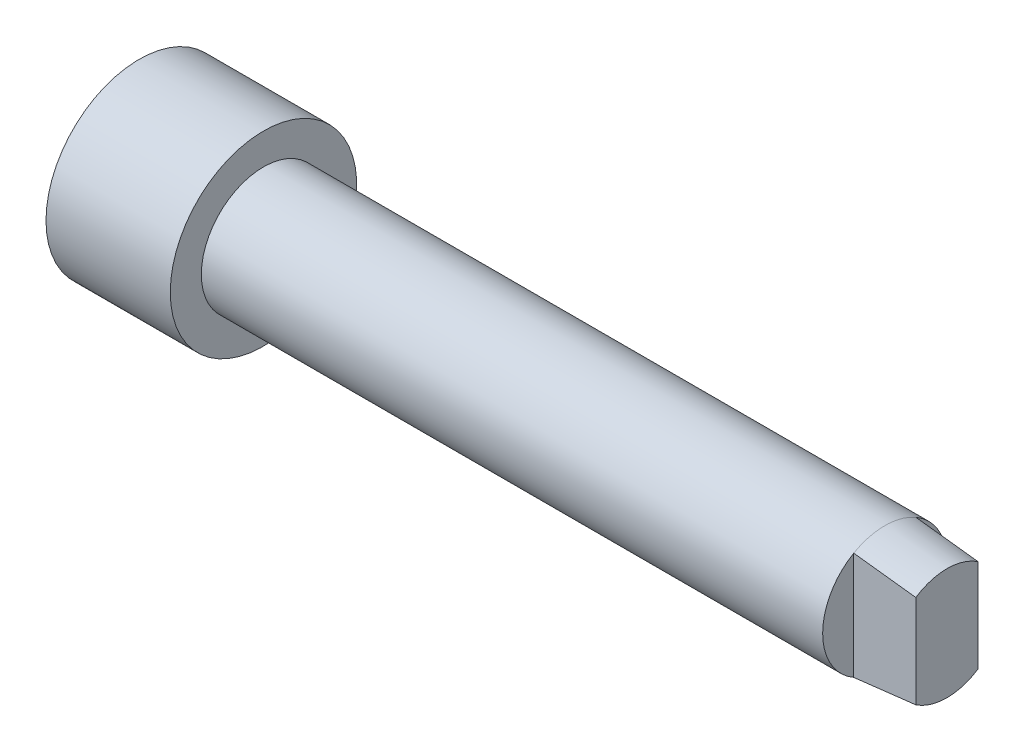
SolidWorks part; units mm, degrees
ref_plane "Front Plane" through (0, 0, 0) normal (0, 0, 1) x (1, 0, 0)
ref_plane "Top Plane" through (0, 0, 0) normal (0, 1, 0) x (1, 0, 0)
ref_plane "Right Plane" through (0, 0, 0) normal (1, 0, 0) x (0, 0, -1)
sketch "Sketch1" plane through (0, 0, 0) normal (0, 0, 1) x (1, 0, 0)
  line L0 (0, 0) -> (55, 0)
  line L1 (55, 0) -> (55, 4.5)
  line L2 (55, 4.5) -> (50, 5)
  line L3 (50, 5) -> (0, 5)
  line L4 (0, 5) -> (0, 0)
  line L5 (0, 5) -> (0, 7.5)
  line L6 (0, 7.5) -> (-10, 7.5)
  line L7 (-10, 7.5) -> (-10, 5)
  line L8 (-10, 5) -> (-5, 5)
  line L9 (-5, 5) -> (-5, 0)
  line L10 (-5, 0) -> (0, 0)
  dimension "D1" = 55
  dimension "D2" = 4.5
  dimension "D3" = 5
  dimension "D4" = 5
  dimension "D5" = 2.5
  dimension "D6" = 10
  dimension "D7" = 5
revolve "Revolve1" add sketch "Sketch1" angle 360 about L0
sketch "Sketch2" plane through (55, 0, 0) normal (1, 0, 0) x (0, 0, -1)
  line L0 (-2.5, -4.3301) -> (-2.5, 4.3301)
  line L1 (2.5, 4.3301) -> (2.5, -4.3301)
  line L2 (-2.5, -4.3301) -> (-5, -4.3301)
  line L3 (-5, -4.3301) -> (-5, 4.3301)
  line L4 (-5, 4.3301) -> (-2.5, 4.3301)
  line L5 (2.5, 4.3301) -> (5, 4.3301)
  line L6 (5, 4.3301) -> (5, -4.3301)
  line L7 (5, -4.3301) -> (2.5, -4.3301)
  circle A0 centre (0, 0) radius 5 construction
  circle A1 centre (0, 0) radius 5 construction
  dimension "D1" = 5
extrude "Cut-Extrude1" cut sketch "Sketch2" against normal blind 5
